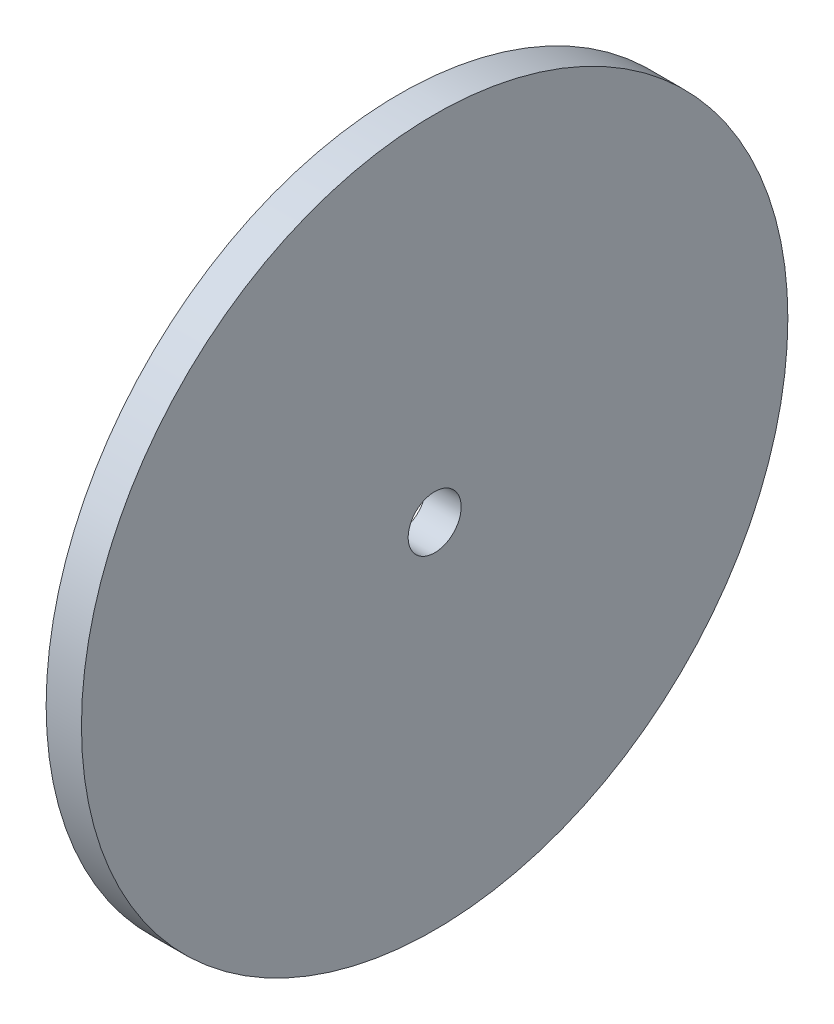
SolidWorks part; units mm, degrees
material "Pine"
ref_plane "Front Plane" through (0, 0, 0) normal (0, 0, 1) x (1, 0, 0)
ref_plane "Top Plane" through (0, 0, 0) normal (0, 1, 0) x (1, 0, 0)
ref_plane "Right Plane" through (0, 0, 0) normal (1, 0, 0) x (0, 0, -1)
sketch "Sketch1" plane through (0, 0, 0) normal (1, 0, 0) x (0, 0, -1)
  circle A0 centre (0, 0) radius 20
  dimension "D1" = 40
extrude "Boss-Extrude1" add sketch "Sketch1" along normal blind 2
sketch "Sketch2" plane through (2, 0, 0) normal (1, 0, 0) x (0, 0, -1)
  circle A1 centre (0, 0) radius 1.5
extrude "Cut-Extrude1" cut sketch "Sketch2" against normal through all
